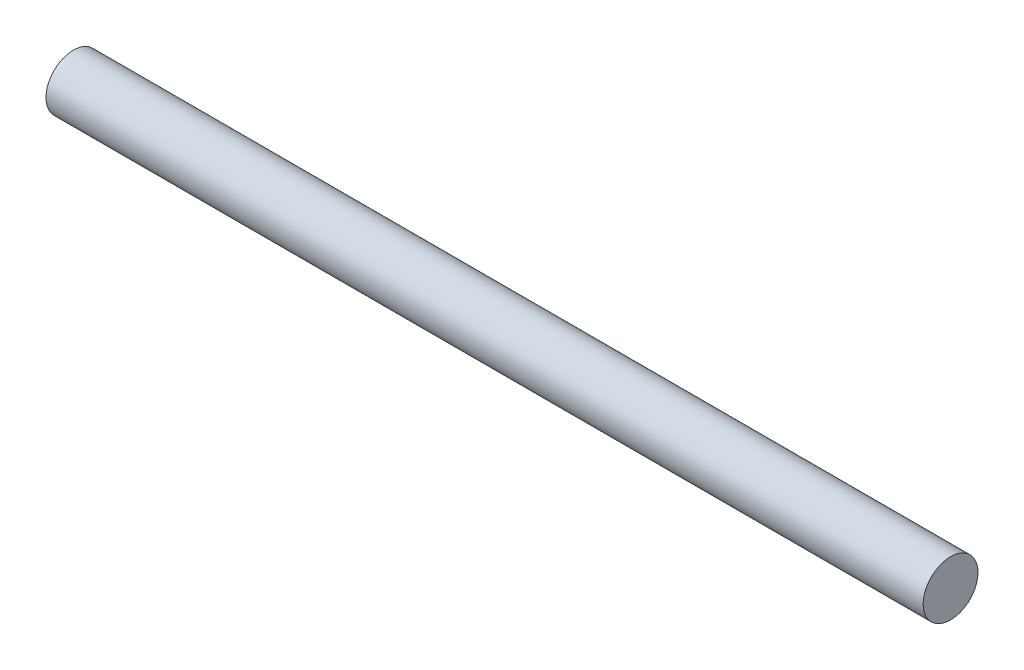
SolidWorks part; units mm, degrees
ref_plane "Front Plane" through (0, 0, 0) normal (0, 0, 1) x (1, 0, 0)
ref_plane "Top Plane" through (0, 0, 0) normal (0, 1, 0) x (1, 0, 0)
ref_plane "Right Plane" through (0, 0, 0) normal (1, 0, 0) x (0, 0, -1)
sketch "Sketch1" plane through (0, 0, 0) normal (1, 0, 0) x (0, 0, -1)
  circle A0 centre (0, 0) radius 2.3813
  dimension "D1" = 4.7625
extrude "Boss-Extrude1" add sketch "Sketch1" along normal blind 76.2
